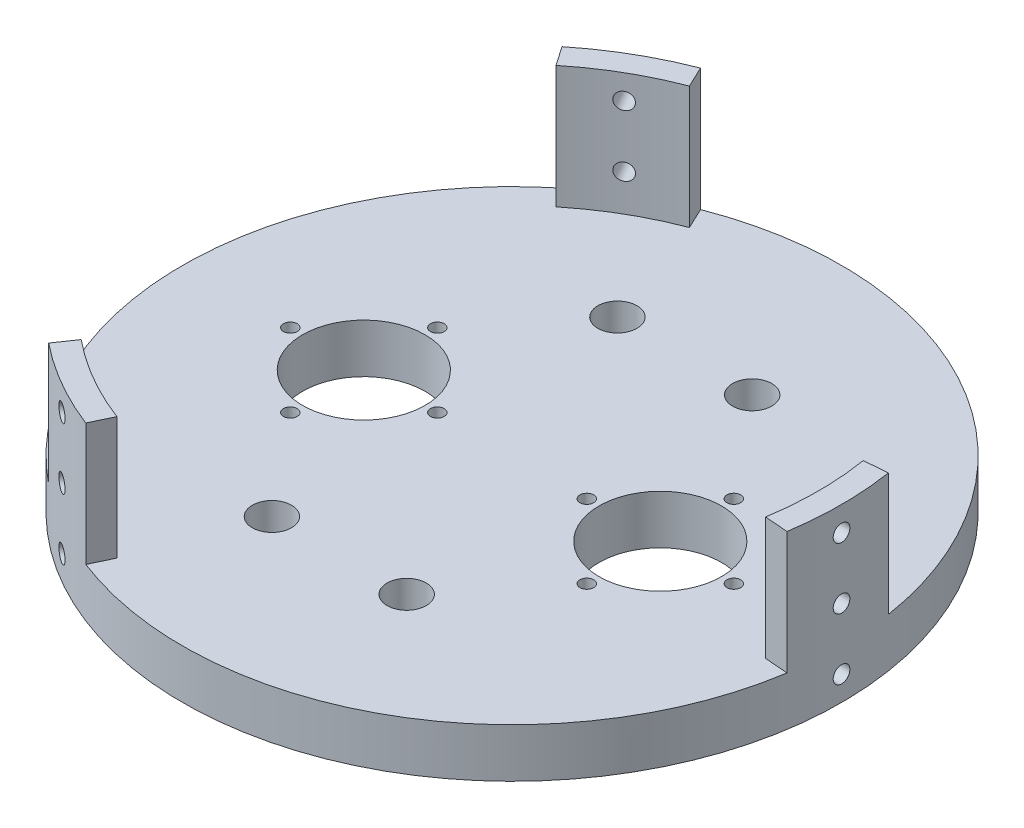
SolidWorks part; units mm, degrees
material "6061-T6 (SS)"
ref_plane "Front" through (0, 0, 0) normal (0, 0, 1) x (1, 0, 0)
ref_plane "Top" through (0, 0, 0) normal (0, 1, 0) x (1, 0, 0)
ref_plane "Right" through (0, 0, 0) normal (1, 0, 0) x (0, 0, -1)
sketch "Sketch1" plane through (0, 0, 0) normal (0, 1, 0) x (1, 0, 0)
  line L1 (0, 0) -> (127.635, 0)
  line L2 (0, 0) -> (0, 127.635)
  line L3 (0, 127.635) -> (127.635, 127.635)
  line L4 (127.635, 0) -> (127.635, 127.635)
  dimension "D1" = 127.635
  dimension "D2" = 127.635
extrude "Main Plate" add sketch "Sketch1" along normal blind 12.7
sketch "Sketch9" plane through (0, 12.7, 0) normal (0, 1, 0) x (1, 0, 0)
  circle A0 centre (63.8175, 63.8175) radius 85.725
  dimension "D1" = 171.45
extrude "Boss-Extrude1" add sketch "Sketch9" against normal up to surface (12.7 mm away) contours A0 up to face at (63.8175, 0, -63.8175)
sketch "Sketch10" plane through (0, 12.7, 0) normal (0, 1, 0) x (1, 0, 0)
  circle A0 centre (63.8175, 63.8175) radius 95.25
  circle A1 centre (63.8175, 63.8175) radius 85.4075
  dimension "D1" = 170.815
  dimension "D2" = 190.5
extrude "Cut-Extrude1" cut sketch "Sketch10" against normal blind 167.64 contours A0 | A1
sketch "Sketch14" plane through (0, 12.7, 0) normal (0, 1, 0) x (1, 0, 0)
  line L0 (201.1692, 63.8175) -> (-73.4523, 63.8175) construction
ref_plane "Plane1" through (0, 0, -63.8175) normal (0, 0, -1) x (-1, 0, 0)
ref_plane "Plane3" through (0, 6.35, 0) normal (0, 1, 0) x (1, 0, 0)
ref_plane "Plane2" through (-21.59, 0, 0) normal (-1, 0, 0) x (0, 0, 1)
sketch "Sketch18" plane through (0, 6.35, 0) normal (0, 1, 0) x (1, 0, 0)
  circle A0 centre (63.8175, 63.8175) radius 85.4075
  circle A1 centre (63.8175, 63.8175) radius 79.375
  circle A4 centre (63.8175, 63.8175) radius 85.4075 construction
  dimension "D1" = 158.75
extrude "Boss-Extrude2" add sketch "Sketch18" along normal blind 38.1
sketch "Sketch20" plane through (0, 12.7, 0) normal (0, 1, 0) x (1, 0, 0)
  line L0 (63.8175, 143.1925) -> (63.8175, -15.5575) construction
  line L1 (-15.5575, 63.8175) -> (143.1925, 63.8175) construction
  line L2 (63.8175, 63.8175) -> (-15.5575, -73.664) construction
  circle A0 centre (63.8175, 63.8175) radius 79.375 construction
  dimension "D1" = 30
ref_plane "Plane5" through (-15.5575, 12.7, 73.664) normal (-0.5, 0, 0.866) x (0.866, 0, 0.5)
sketch "Sketch15" plane through (166.2216, 0, 178.6143) normal (0.5, 0, -0.866) x (-0.866, 0, -0.5)
  line L3 (289.2754, 44.45) -> (130.5254, 44.45) construction
  line L4 (124.4929, 0) -> (295.3079, 0) construction
  line L6 (278.6412, 12.7) -> (141.1597, 12.7) construction
  circle A0 centre (209.9004, 22.225) radius 2.159
  circle A1 centre (209.9004, 38.1) radius 2.159
  circle A2 centre (209.9004, 6.35) radius 2.159
  point P16 (209.9004, 12.7)
  dimension "D1" = 4.318
  dimension "D2" = 15.875
  dimension "D3" = 4.318
  dimension "D4" = 4.318
  dimension "D5" = 6.35
  dimension "D6" = 6.35
  dimension "D7" = 0
extrude "Cut-Extrude3" cut sketch "Sketch15" along normal blind 88.9
pattern_circular "CirPattern1" count 3 over 360 about axis through (63.8175, 0, -63.8175) along (0, 1, 0) of "Cut-Extrude3"
ref_plane "Plane4" through (63.8175, 0, 0) normal (-1, 0, 0) x (0, 0, 1)
sketch "Sketch21" plane through (0, 12.7, 0) normal (0, 1, 0) x (1, 0, 0)
  line L1 (-15.5575, 63.8175) -> (143.1925, 63.8175) construction
  line L2 (102.235, 63.8175) -> (102.235, 100.651) construction
  line L3 (63.8175, 87.3125) -> (63.8175, -87.3125) construction
  circle A0 centre (102.235, 63.8175) radius 15.875
  circle A1 centre (102.235, 82.8675) radius 1.778
  circle A2 centre (25.4, 63.8175) radius 15.875
  circle A3 centre (121.285, 63.8175) radius 1.778
  circle A4 centre (102.235, 44.7675) radius 1.778
  circle A5 centre (83.185, 63.8175) radius 1.778
  circle A6 centre (25.4, 82.8675) radius 1.778
  circle A7 centre (6.35, 63.8175) radius 1.778
  circle A8 centre (25.4, 44.7675) radius 1.778
  circle A9 centre (44.45, 63.8175) radius 1.778
  dimension "D1" = 31.75
  dimension "D2" = 3.556
  dimension "D6" = 19.05
  dimension "D3" = 19.05
  dimension "D4" = 76.835
  dimension "D7" = 19.05
  dimension "D5" = 4
extrude "CO2 Mounts" cut sketch "Sketch21" against normal through all
sketch "Sketch22" plane through (0, 12.7, 0) normal (0, 1, 0) x (1, 0, 0)
  line L0 (63.8175, 87.3125) -> (63.8175, -87.3125) construction
  line L1 (87.3125, 63.8175) -> (-87.3125, 63.8175) construction
  circle A0 centre (46.355, 108.585) radius 5.08
  circle A1 centre (81.28, 108.585) radius 5.08
  circle A2 centre (81.28, 19.05) radius 5.08
  circle A3 centre (46.355, 19.05) radius 5.08
  dimension "D1" = 10.16
  dimension "D2" = 34.925
  dimension "D3" = 89.535
extrude "Cut-Extrude5" cut sketch "Sketch22" against normal through all
sketch "Sketch23" plane through (0, 12.7, 0) normal (0, 1, 0) x (1, 0, 0)
  line L0 (13.6787, 125.352) -> (7.5523, 134.2379)
  line L1 (15.1867, 11.8815) -> (13.6787, 2.283) construction
  line L3 (-15.5575, 63.8175) -> (143.1925, 63.8175) construction
  line L4 (63.8175, 143.1925) -> (63.8175, -15.5575) construction
  line L5 (-15.5575, 63.8175) -> (143.1925, 63.8175)
  line L6 (63.8175, 143.1925) -> (63.8175, -15.5575)
  line L7 (13.6787, 2.283) -> (6.9592, -7.4631)
  line L8 (-19.2671, 125.3206) -> (-48.797, 60.3978)
  line L9 (-48.797, 60.3978) -> (-9.8843, 7.0525)
  line L10 (-9.8843, 7.0525) -> (6.9592, -7.4631)
  line L11 (24.1345, -4.9259) -> (13.6787, 2.283) construction
  line L14 (7.5523, 134.2379) -> (-19.2671, 125.3206)
  line L15 (24.1345, 132.5609) -> (13.6787, 125.352) construction
  line L28 (63.8175, 63.8175) -> (24.1345, -4.9259) construction
  line L29 (63.8175, 63.8175) -> (24.1345, 132.5609) construction
  line L30 (142.1773, 76.4717) -> (152.9359, 77.3344)
  line L31 (152.9359, 77.3344) -> (158.6231, 105.0193)
  line L32 (158.6231, 105.0193) -> (117.1632, 163.0543)
  line L33 (117.1632, 163.0543) -> (51.5085, 156.0277)
  line L34 (51.5085, 156.0277) -> (30.5159, 148.6985)
  line L35 (35.5964, 138.0062) -> (30.5159, 148.6985)
  line L36 (35.5964, -10.3712) -> (30.9643, -20.1198)
  line L37 (30.9643, -20.1198) -> (52.0965, -38.8874)
  line L38 (52.0965, -38.8874) -> (123.0863, -31.9996)
  line L39 (123.0863, -31.9996) -> (149.8284, 28.3723)
  line L40 (149.8284, 28.3723) -> (153.9775, 50.217)
  line L41 (142.1773, 51.1633) -> (153.9775, 50.217)
  circle A0 centre (63.8175, 63.8175) radius 79.375 construction
  arc A1 (13.6787, 2.283) -> (13.6787, 125.352) centre (63.8175, 63.8175) cw
  circle A3 centre (63.8175, 63.8175) radius 79.375
  arc A6 (35.5964, 138.0062) -> (142.1773, 76.4717) centre (63.8175, 63.8175) cw
  arc A7 (142.1773, 51.1633) -> (35.5964, -10.3712) centre (63.8175, 63.8175) cw
  circle A9 centre (63.8175, 63.8175) radius 79.375
  dimension "D1" = 79.375
  dimension "D2" = 0
  dimension "D3" = 12.7
  dimension "D4" = 90
  dimension "D5" = 12.7
  dimension "D6" = 90
  dimension "D8" = 60.004
  dimension "D9" = 60.004
  dimension "D7" = 3
extrude "Cut-Extrude6" cut sketch "Sketch23" along normal blind 111.6
